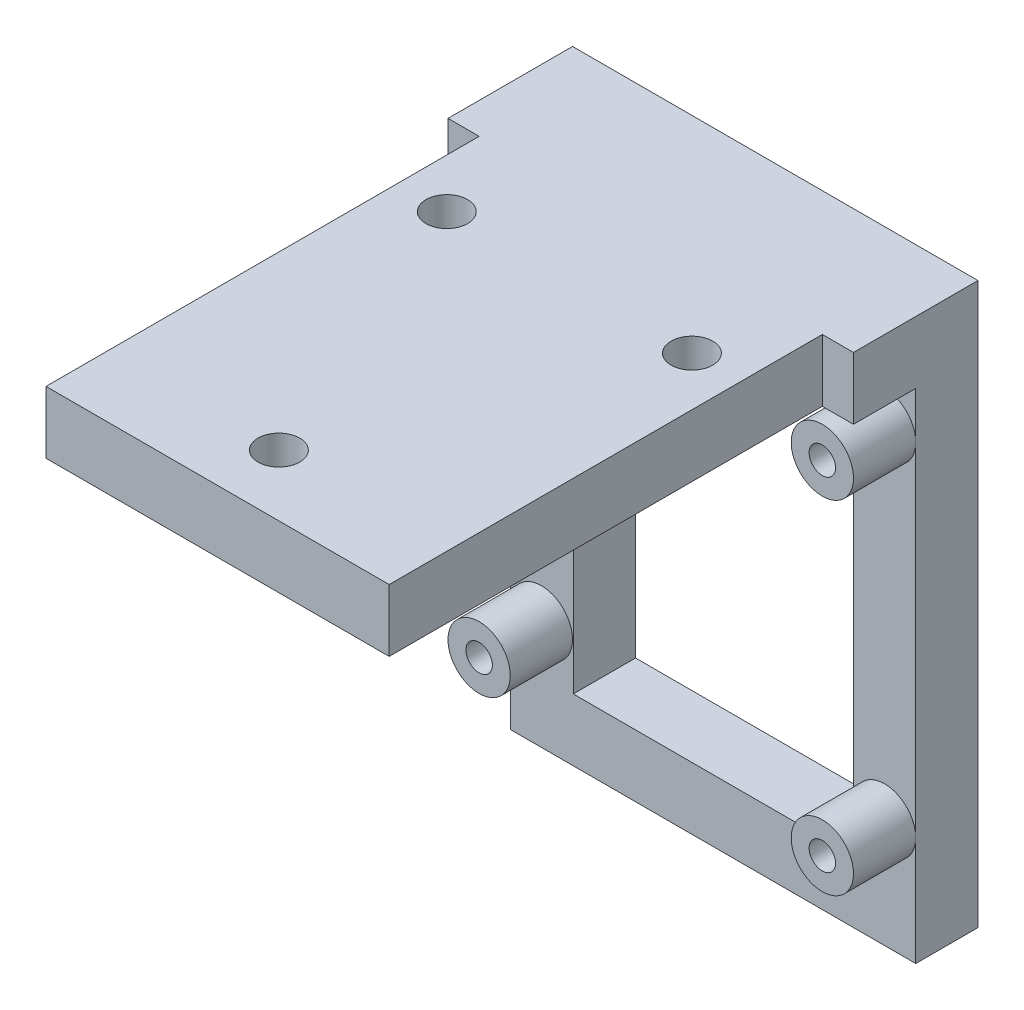
SolidWorks part; units mm, degrees
ref_plane "Front Plane" through (0, 0, 0) normal (0, 0, 1) x (1, 0, 0)
ref_plane "Top Plane" through (0, 0, 0) normal (0, 1, 0) x (1, 0, 0)
ref_plane "Right Plane" through (0, 0, 0) normal (1, 0, 0) x (0, 0, -1)
sketch "Sketch1" plane through (0, 0, 0) normal (0, 1, 0) x (1, 0, 0)
  line L1 (0, 0) -> (33.08, 0)
  line L2 (0, 0) -> (0, 45.5)
  line L3 (0, 45.5) -> (33.08, 45.5)
  line L4 (33.08, 0) -> (33.08, 45.5)
  dimension "D1" = 33.08
  dimension "D2" = 45.5
extrude "Boss-Extrude1" add sketch "Sketch1" along normal blind 5.08
sketch "Sketch2" plane through (0, 0, 0) normal (0, -1, 0) x (1, 0, 0)
  line L2 (0, 0) -> (33.08, 0) construction
  circle A0 centre (6.54, -28.7) radius 1.7
  circle A3 centre (26.54, -28.7) radius 1.7
  circle A4 centre (16.54, -5) radius 1.7
  point P9 (16.54, 0)
  dimension "D1" = 3.4
  dimension "D2" = 3.4
  dimension "D3" = 3.4
  dimension "D4" = 20
  dimension "D5" = 23.7
  dimension "D6" = 10
  dimension "D8" = 5
extrude "Cut-Extrude1" cut sketch "Sketch2" against normal through all
sketch "Sketch3" plane through (0, 0, 0) normal (0, -1, 0) x (1, 0, 0)
  line L0 (0, -45.5) -> (0, 0) construction
  line L1 (33.08, -45.5) -> (0, -45.5)
  line L2 (33.08, -45.5) -> (33.08, -40.42)
  line L3 (33.08, -40.42) -> (0, -40.42)
  line L4 (0, -45.5) -> (0, -40.42)
  dimension "D1" = 5.08
extrude "Boss-Extrude2" add sketch "Sketch3" along normal blind 40.64
sketch "Sketch4" plane through (0, 0, -40.42) normal (0, 0, 1) x (1, 0, 0)
  line L0 (33.08, -40.64) -> (0, -40.64) construction
  line L1 (28, -35.56) -> (5.14, -35.56)
  line L2 (28, -35.56) -> (28, 0)
  line L3 (28, 0) -> (5.14, 0)
  line L4 (5.14, -35.56) -> (5.14, 0)
  line L5 (33.08, -40.64) -> (33.08, 0) construction
  line L6 (0, -40.64) -> (0, 0) construction
  circle A0 centre (30.54, -31.75) radius 1.0795
  circle A1 centre (2.54, -31.75) radius 1.0795
  circle A2 centre (30.54, -3.81) radius 1.0795
  circle A3 centre (2.54, -3.81) radius 1.0795
  dimension "D5" = 2.159
  dimension "D6" = 2.159
  dimension "D7" = 2.159
  dimension "D8" = 2.159
  dimension "D10" = 27.94
  dimension "D1" = 22.86
  dimension "D2" = 35.56
  dimension "D3" = 5.08
  dimension "D4" = 5.08
  dimension "D9" = 8.89
  dimension "D11" = 2.54
  dimension "D12" = 2.54
extrude "Cut-Extrude2" cut sketch "Sketch4" against normal through all both and the other way through all
sketch "Sketch5" plane through (0, 0, -40.42) normal (0, 0, 1) x (1, 0, 0)
  circle A0 centre (30.54, -31.75) radius 2.54
  circle A1 centre (30.54, -3.81) radius 2.54
  circle A2 centre (2.54, -3.81) radius 2.54
  circle A3 centre (2.54, -31.75) radius 2.54
  circle A4 centre (30.54, -31.75) radius 1.0795
  circle A5 centre (2.54, -31.75) radius 1.0795
  circle A6 centre (30.54, -3.81) radius 1.0795
  circle A7 centre (2.54, -3.81) radius 1.0795
extrude "Boss-Extrude3" add sketch "Sketch5" along normal blind 5.08
sketch "Sketch6" plane through (0, 0, 0) normal (0, -1, 0) x (1, 0, 0)
  line L1 (0, 0) -> (2.54, 0)
  line L2 (0, 0) -> (0, -35.34)
  line L3 (0, -35.34) -> (2.54, -35.34)
  line L4 (2.54, 0) -> (2.54, -35.34)
  line L5 (33.08, 0) -> (30.54, 0)
  line L6 (33.08, 0) -> (33.08, -35.34)
  line L7 (33.08, -35.34) -> (30.54, -35.34)
  line L8 (30.54, 0) -> (30.54, -35.34)
  line L9 (5.08, -35.34) -> (0, -35.34) construction
  line L10 (33.08, -35.34) -> (28, -35.34) construction
  dimension "D1" = 2.54
  dimension "D2" = 2.54
extrude "Cut-Extrude3" cut sketch "Sketch6" against normal through all
